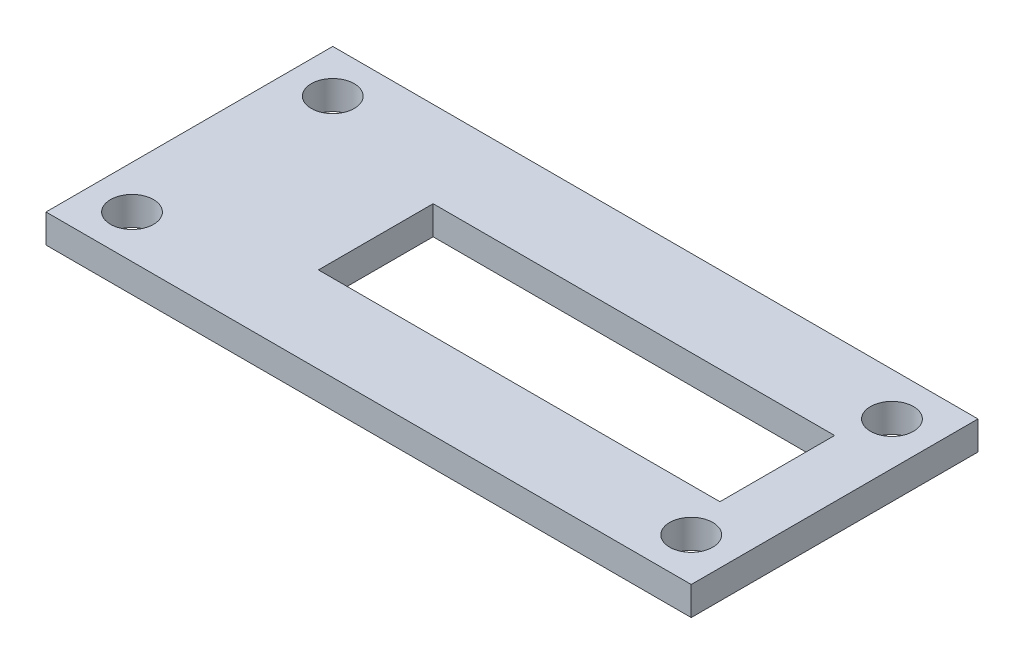
SolidWorks part; units mm, degrees
ref_plane "Alzado" through (0, 0, 0) normal (0, 0, 1) x (1, 0, 0)
ref_plane "Planta" through (0, 0, 0) normal (0, 1, 0) x (1, 0, 0)
ref_plane "Vista lateral" through (0, 0, 0) normal (1, 0, 0) x (0, 0, -1)
sketch "Croquis2" plane through (0, 0, 0) normal (0, 1, 0) x (1, 0, 0)
  line L1 (-22.5, -10) -> (22.5, -10)
  line L2 (-22.5, -10) -> (-22.5, 10)
  line L3 (-22.5, 10) -> (22.5, 10)
  line L4 (22.5, -10) -> (22.5, 10)
  line L5 (-22.5, -10) -> (22.5, 10) construction
  line L6 (-22.5, 10) -> (22.5, -10) construction
  point P0 (0, 0)
  dimension "D1" = 45
  dimension "D2" = 20
extrude "Saliente-Extruir1" add sketch "Croquis2" along normal blind 2
sketch "Croquis3" plane through (0, 2, 0) normal (0, 1, 0) x (1, 0, 0)
  line L0 (0, 0) -> (0, 10.6636) construction
  line L1 (-19.5, 10) -> (-19.5, 7) construction
  line L2 (0, 0) -> (6.9426, 0) construction
  line L3 (-22.5, 10) -> (-19.5, 10) construction
  line L5 (22.5, 10) -> (-22.5, 10) construction
  circle A4 centre (-19.5, 7) radius 1.5
  circle A5 centre (19.5, 7) radius 1.5
  circle A6 centre (-19.5, -7) radius 1.5
  circle A7 centre (19.5, -7) radius 1.5
  point P16 (-19.4804, 7)
extrude "Cortar-Extruir1" cut sketch "Croquis3" against normal through all
sketch "Croquis4" plane through (0, 2, 0) normal (0, 1, 0) x (1, 0, 0)
  line L0 (-22.5, 0) -> (-9.5, 0) construction
  line L1 (-22.5, 10) -> (-22.5, -10) construction
  line L2 (-9.5, 4) -> (-9.5, -4)
  line L3 (-9.5, -4) -> (18.5, -4)
  line L4 (18.5, -4) -> (18.5, 4)
  line L5 (18.5, 4) -> (-9.5, 4)
  point P8 (-9.5, 0)
extrude "Cortar-Extruir2" cut sketch "Croquis4" against normal through all
